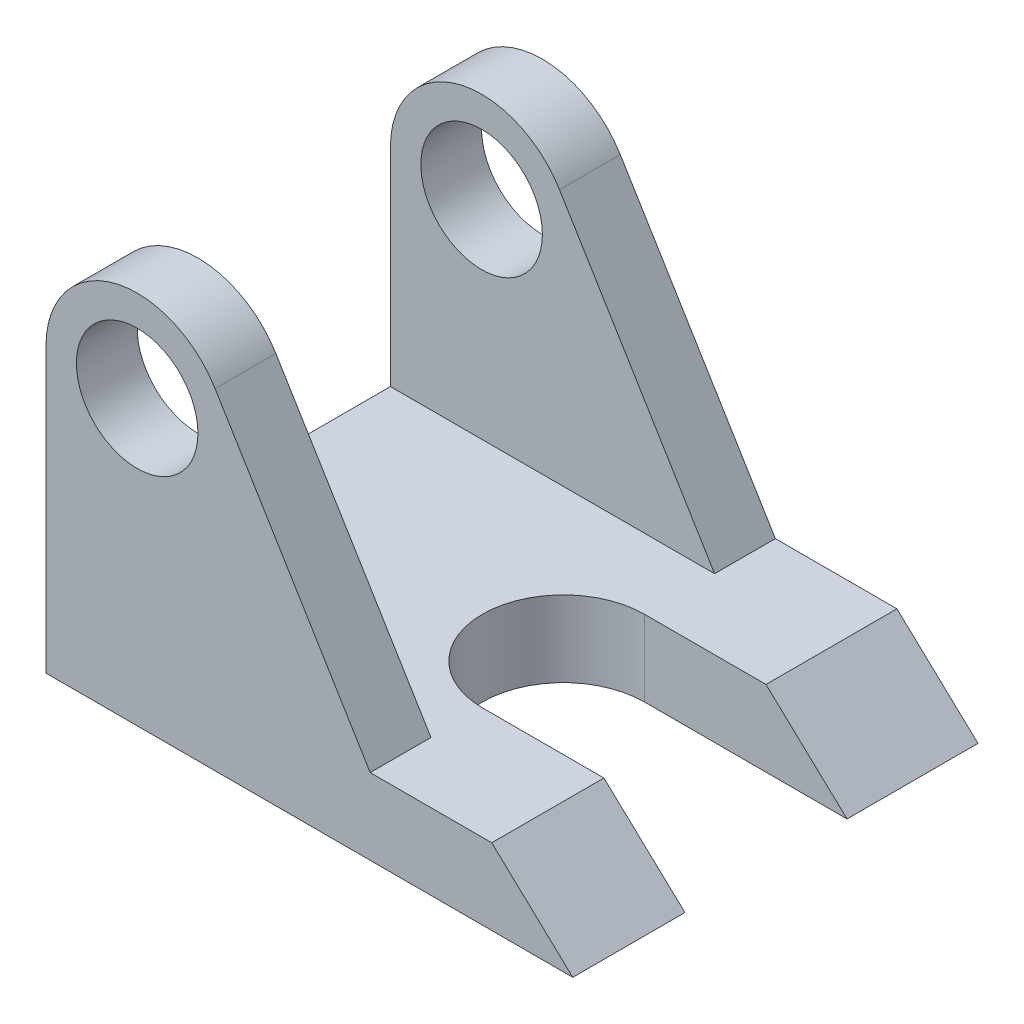
SolidWorks part; units mm, degrees
ref_plane "Front Plane" through (0, 0, 0) normal (0, 0, 1) x (1, 0, 0)
ref_plane "Top Plane" through (0, 0, 0) normal (0, 1, 0) x (1, 0, 0)
ref_plane "Right Plane" through (0, 0, 0) normal (1, 0, 0) x (0, 0, -1)
sketch "Sketch1" plane through (0, 0, 0) normal (0, 0, 1) x (1, 0, 0)
  line L0 (-49.6332, 65.6005) -> (-49.6332, -4.3995)
  line L1 (-49.6332, -4.3995) -> (80.3668, -4.3995)
  line L2 (80.3668, -4.3995) -> (60.3668, 14.3582)
  line L3 (60.3668, 14.3582) -> (30.3668, 14.3582)
  line L4 (30.3668, 14.3582) -> (-7.9094, 77.2923)
  arc A0 (-7.9094, 77.2923) -> (-49.6332, 65.6005) centre (-27.1332, 65.6005) ccw
  circle A1 centre (-27.1332, 65.6005) radius 15
  dimension "D1" = 45
  dimension "D6" = 30
  dimension "D2" = 70
  dimension "D3" = 130
  dimension "D4" = 20
  dimension "D5" = 30
extrude "Boss-Extrude1" add sketch "Sketch1" against normal blind 100
sketch "Sketch3" plane through (0, 0, 0) normal (1, 0, 0) x (0, 0, -1)
  line L0 (100, 88.1005) -> (0, 88.1005) construction
  line L1 (15, 88.1005) -> (85, 88.1005)
  line L2 (15, 88.1005) -> (15, 14.3582)
  line L3 (15, 14.3582) -> (85, 14.3582)
  line L4 (85, 88.1005) -> (85, 14.3582)
  line L5 (100, 14.3582) -> (0, 14.3582) construction
  line L6 (0, 14.3582) -> (0, 77.2923) construction
  dimension "D1" = 70
  dimension "D2" = 15
extrude "Cut-Extrude1" cut sketch "Sketch3" against normal mid plane 100
sketch "Sketch4" plane through (0, 14.3582, 0) normal (0, 1, 0) x (1, 0, 0)
  line L0 (80.3668, 100) -> (80.3668, 0) construction
  line L2 (30.3668, 67.6839) -> (82.7082, 67.6839)
  line L4 (30.3668, 27.6839) -> (82.7082, 27.6839)
  line L5 (82.7082, 67.6839) -> (82.7082, 27.6839)
  arc A0 (30.3668, 67.6839) -> (30.3668, 27.6839) centre (30.3668, 47.6839) ccw
  dimension "D2" = 40
  dimension "D1" = 50
extrude "Cut-Extrude2" cut sketch "Sketch4" against normal mid plane 40
